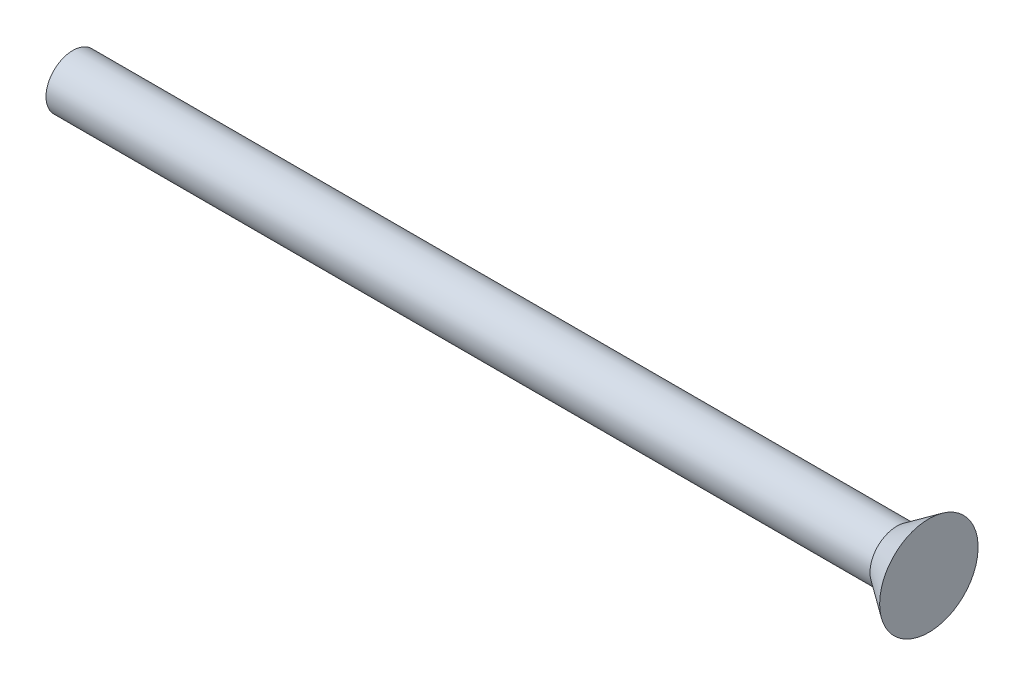
SolidWorks part; units mm, degrees
material "1060 合金"
ref_plane "前视基准面" through (0, 0, 0) normal (0, 0, 1) x (1, 0, 0)
ref_plane "上视基准面" through (0, 0, 0) normal (0, 1, 0) x (1, 0, 0)
ref_plane "右视基准面" through (0, 0, 0) normal (1, 0, 0) x (0, 0, -1)
sketch "草图1" plane through (0, 0, 0) normal (0, 0, 1) x (1, 0, 0)
  line L0 (-53.8441, 0) -> (16.0999, 0) construction
  line L1 (-30, 0) -> (-30, 1.25)
  line L2 (-30, 1.25) -> (8.5, 1.25)
  line L3 (8.5, 1.25) -> (10, 2.3)
  line L4 (-30, 0) -> (10, 0)
  line L5 (10, 2.3) -> (10, 0)
  dimension "D1" = 2.5
  dimension "D2" = 40
  dimension "D3" = 1.5
  dimension "D4" = 4.6
  dimension "D5" = 10
revolve "旋转1" add sketch "草图1" angle 360 about L0
cosmetic thread "装饰螺纹线1" parameters "D2"=2.013
